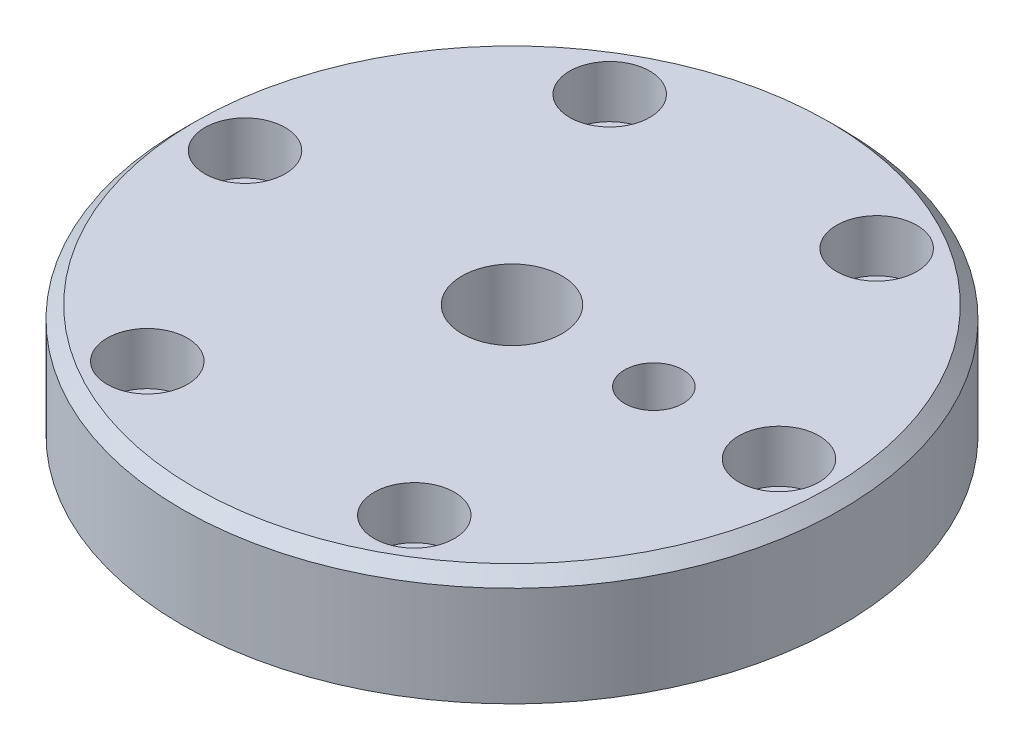
SolidWorks part; units mm, degrees
ref_plane "Front Plane" through (0, 0, 0) normal (0, 0, 1) x (1, 0, 0)
ref_plane "Top Plane" through (0, 0, 0) normal (0, 1, 0) x (1, 0, 0)
ref_plane "Right Plane" through (0, 0, 0) normal (1, 0, 0) x (0, 0, -1)
sketch "Sketch1" plane through (0, 0, 0) normal (0, 1, 0) x (1, 0, 0)
  circle A0 centre (0, 0) radius 79
  circle A1 centre (0, 0) radius 12
  dimension "D1" = 158
  dimension "D2" = 12
extrude "Boss-Extrude1" add sketch "Sketch1" along normal blind 27
sketch "Sketch13" plane through (0, 27, 0) normal (0, 1, 0) x (1, 0, 0)
  line L0 (0, 0) -> (24.7367, 42.8452) construction
  circle A0 centre (0, 0) radius 64 construction
hole_wizard "CBORE for M5 Hex Head Bolt6" positions "Sketch16" profile "Sketch17" counterbore size "M5" standard "ANSI Metric" end condition through all
sketch "Sketch16" plane through (0, 27, 0) normal (0, 1, 0) x (1, 0, 0)
  line L0 (-100000, -173205.0808) -> (100024.7367, 173247.9259) construction
  circle A0 centre (0, 0) radius 64 construction
  point P0 (32, 55.4256)
  dimension "D1" = 64
sketch "Sketch17" plane through (32, 27, -55.4256) normal (1, 0, 0) x (0, 0, 1)
  line L0 (0, 0) -> (0, 27)
  line L1 (0, 27) -> (6.25, 27)
  line L3 (6.25, 27) -> (6.25, 12.5)
  line L4 (6.25, 12.5) -> (9.625, 12.5)
  line L5 (9.625, 12.5) -> (9.625, 0)
  line L7 (9.625, 0) -> (0, 0)
  line L11 (0, -6.35) -> (0, 107.95) construction
  dimension "Thru Hole Dia." = 12.5
  dimension "Thru Hole Depth" = 27
  dimension "C'Bore Dia." = 19.25
  dimension "C'Bore Depth" = 12.5
pattern_circular "CirPattern1" count 6 over 360 about axis through (0, 0, 0) along (0, 1, 0) of "CBORE for M5 Hex Head Bolt6"
hole_wizard "Ø1.0mm Dowel Hole1" positions "Sketch18" profile "Sketch19" hole size "Ø1.0" standard "ANSI Metric"
sketch "Sketch18" plane through (0, 27, 0) normal (0, 1, 0) x (1, 0, 0)
  point P0 (34, 0)
  dimension "D1" = 34
sketch "Sketch19" plane through (34, 27, 0) normal (1, 0, 0) x (0, 0, 1)
  line L0 (0, 0) -> (0, 21.206)
  line L1 (0, 21.206) -> (7, 17)
  line L2 (7, 17) -> (7, 0)
  line L5 (7, 0) -> (0, 0)
  line L10 (0, 21.206) -> (-7, 17) construction
  line L11 (0, -6.35) -> (0, 107.95) construction
  dimension "Hole Dia." = 14
  dimension "Hole Depth" = 17
  dimension "Drill Angle" = 118
sketch "Sketch20" plane through (0, 0, 0) normal (0, 1, 0) x (1, 0, 0)
  circle A0 centre (0, 0) radius 22
  circle A1 centre (0, 0) radius 33
  dimension "D1" = 11
extrude "Cut-Extrude1" cut sketch "Sketch20" along normal blind 6
chamfer "Chamfer1" distance 3 angle 45 1 edges at (0, 27, 79)
